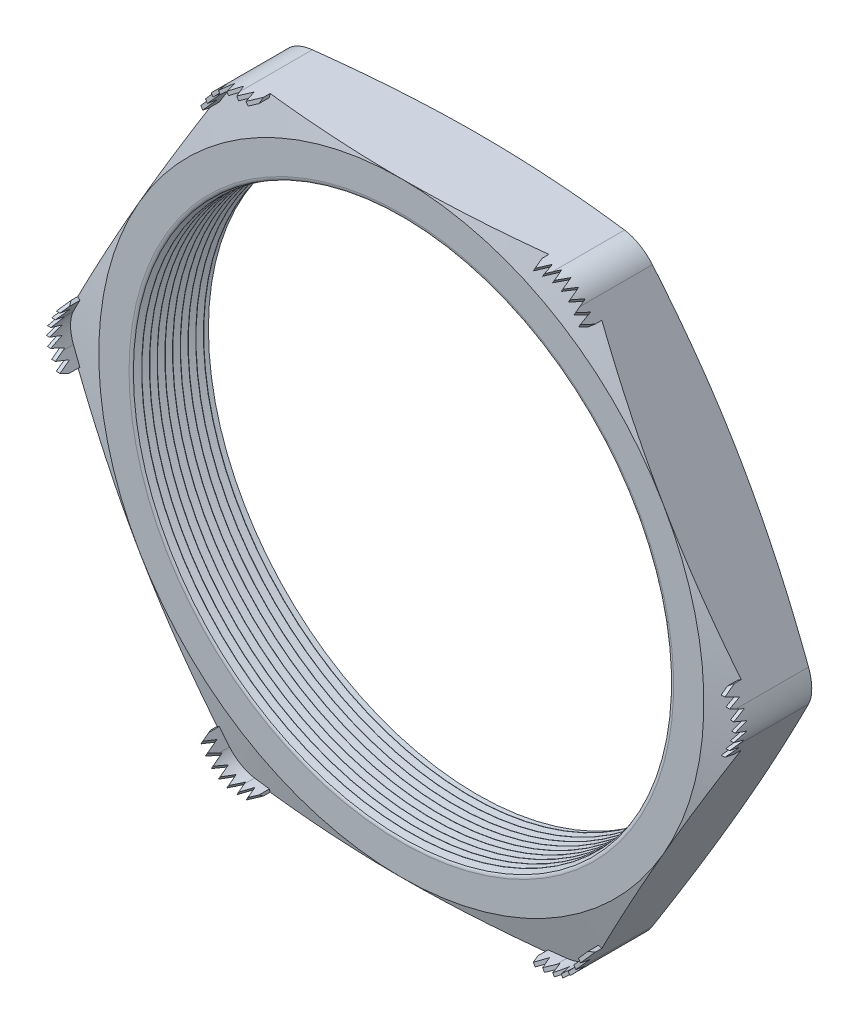
SolidWorks part; units mm, degrees
ref_plane "Front Plane" through (0, 0, 0) normal (0, 0, 1) x (1, 0, 0)
ref_plane "Top Plane" through (0, 0, 0) normal (0, 1, 0) x (1, 0, 0)
ref_plane "Right Plane" through (0, 0, 0) normal (1, 0, 0) x (0, 0, -1)
sketch "Sketch1" plane through (0, 0, 0) normal (0, 0, 1) x (1, 0, 0)
  line L1 (-13.7848, 0) -> (-6.8924, -11.938)
  line L2 (-6.8924, -11.938) -> (6.8924, -11.938)
  line L3 (6.8924, -11.938) -> (13.7848, 0)
  line L4 (13.7848, 0) -> (6.8924, 11.938)
  line L5 (6.8924, 11.938) -> (-6.8924, 11.938)
  line L6 (-6.8924, 11.938) -> (-13.7848, 0)
  circle A0 centre (0, 0) radius 11.938 construction
  circle A1 centre (0, 0) radius 10.541
  dimension "TS" = 21.082
  dimension "H" = 23.876
extrude "Extrude1" add sketch "Sketch1" along normal blind 3.048
fillet "Fillet1" radius 1.27 6 edges at (-6.8924, 11.938, 1.524) (-13.7848, 0, 1.524) (-6.8924, -11.938, 1.524) (6.8924, -11.938, 1.524) (13.7848, 0, 1.524) (6.8924, 11.938, 1.524)
sketch "Sketch2" plane through (0, 0, 3.048) normal (0, 0, 1) x (1, 0, 0)
  line L0 (-6.1592, 11.938) -> (-5.4988, 11.938)
  line L1 (6.1592, 11.938) -> (-6.1592, 11.938) construction
  line L2 (-7.259, 11.303) -> (-7.5892, 10.7311)
  line L3 (-7.259, 11.303) -> (-13.4182, 0.635) construction
  line L4 (-6.1592, 11.811) -> (-5.4988, 11.811)
  line L5 (-7.149, 11.2395) -> (-7.4792, 10.6676)
  line L6 (-7.5892, 10.7311) -> (-7.4792, 10.6676)
  line L7 (-5.4988, 11.938) -> (-5.4988, 11.811)
  arc A0 (-6.1592, 11.811) -> (-7.149, 11.2395) centre (-6.1592, 10.668) ccw
  arc A1 (-6.1592, 11.938) -> (-7.259, 11.303) centre (-6.1592, 10.668) ccw construction
  arc A4 (-6.1592, 11.938) -> (-7.259, 11.303) centre (-6.1592, 10.668) ccw
  dimension "D1" = 0.6604
  dimension "D2" = 0.6604
  dimension "OFFSET" = 0.127
fillet "Fillet3" radius 0.2032 2 edges at (10.541, 0, 0) (10.541, 0, 3.048)
sketch "Sketch3" plane through (0, 0, 0) normal (0, 1, 0) x (1, 0, 0)
  line L0 (-10.541, -3.048) -> (-10.541, -2.7547)
  line L2 (-10.541, -2.7547) -> (-10.795, -2.9014)
  line L3 (-10.795, -2.9014) -> (-10.541, -3.048)
  line L4 (-10.541, -0.2032) -> (-10.541, -2.8448) construction
  line L5 (-7.259, -3.048) -> (-13.4182, -3.048) construction
  dimension "D1" = 60
  dimension "D2" = 60
  dimension "D3" = 0.254
revolve "Cut-Revolve1" cut sketch "Sketch3" angle 360 about axis through (0, 0, 3.048) along (0, 0, -1)
pattern_linear "LPattern1" count 10 spacing 0.3048 along (0, 0, -1) of "Cut-Revolve1"
sketch "Sketch4" plane through (0, 0, 0) normal (0, 0, -1) x (-1, 0, 0)
  line L0 (-13.4182, 0.635) -> (-7.259, 11.303) construction
  circle A0 centre (0, 0) radius 11.938
extrude "Cut-Extrude1" cut sketch "Sketch4" against normal through all draft 75 flip side to cut
sketch "Sketch5" plane through (0, 0, 3.048) normal (0, 0, 1) x (1, 0, 0)
  line L0 (6.1592, 11.938) -> (-6.1592, 11.938) construction
  circle A0 centre (0, 0) radius 11.938
extrude "Cut-Extrude2" cut sketch "Sketch5" against normal through all draft 75 flip side to cut
extrude "Extrude2" add sketch "Sketch2" along normal blind 1.143 and the other way up to next
ref_plane "Plane1" through (-6.489, 11.2393, 0) normal (0.5, -0.866, 0) x (0.866, 0.5, 0)
sketch "Sketch7" plane through (-6.489, 11.2393, 0) normal (0.5, -0.866, 0) x (0.866, 0.5, 0)
  line L0 (-1.2069, 2.9909) -> (-1.0291, 3.4709)
  line L1 (-1.2069, 2.725) -> (-1.2069, 4.191) construction
  line L2 (0, 1.3136) -> (0, 4.0135) construction
  line L4 (-1.0291, 3.4709) -> (-0.8513, 2.9909)
  line L5 (-0.3556, 3.4709) -> (-0.1778, 2.9909)
  line L6 (-0.7112, 3.4709) -> (-0.5334, 2.9909)
  line L7 (-0.1778, 2.9909) -> (0, 3.4709)
  line L8 (0, 3.4709) -> (0.1778, 2.9909)
  line L10 (0.3556, 3.4709) -> (0.5334, 2.9909)
  line L11 (0.7112, 3.4709) -> (0.889, 2.9909)
  line L12 (-0.8513, 2.9909) -> (-0.7112, 3.4709)
  line L13 (-0.5334, 2.9909) -> (-0.3556, 3.4709)
  line L14 (0.1778, 2.9909) -> (0.3556, 3.4709)
  line L15 (1.0291, 3.4709) -> (1.2069, 2.9909)
  line L16 (1.2069, 2.725) -> (1.2069, 4.191) construction
  line L17 (-1.2069, 2.9909) -> (-1.2069, 4.191)
  line L19 (-1.2069, 4.191) -> (1.2069, 4.191)
  line L20 (1.2069, 4.191) -> (1.2069, 2.9909)
  line L23 (0.5334, 2.9909) -> (0.7112, 3.4709)
  line L25 (0.889, 2.9909) -> (1.0291, 3.4709)
  dimension "D1" = 1.2001
  dimension "D2" = 0.7201
  dimension "D3" = 0.1778
extrude "Cut-Extrude4" cut sketch "Sketch7" against normal through all
pattern_circular "CirPattern1" count 6 over 360 about axis through (0, 0, 0) along (0, 0, 1) of "Extrude2"
pattern_circular "CirPattern2" count 6 over 360 about axis through (0, 0, 0) along (0, 0, 1) of "Cut-Extrude4"
